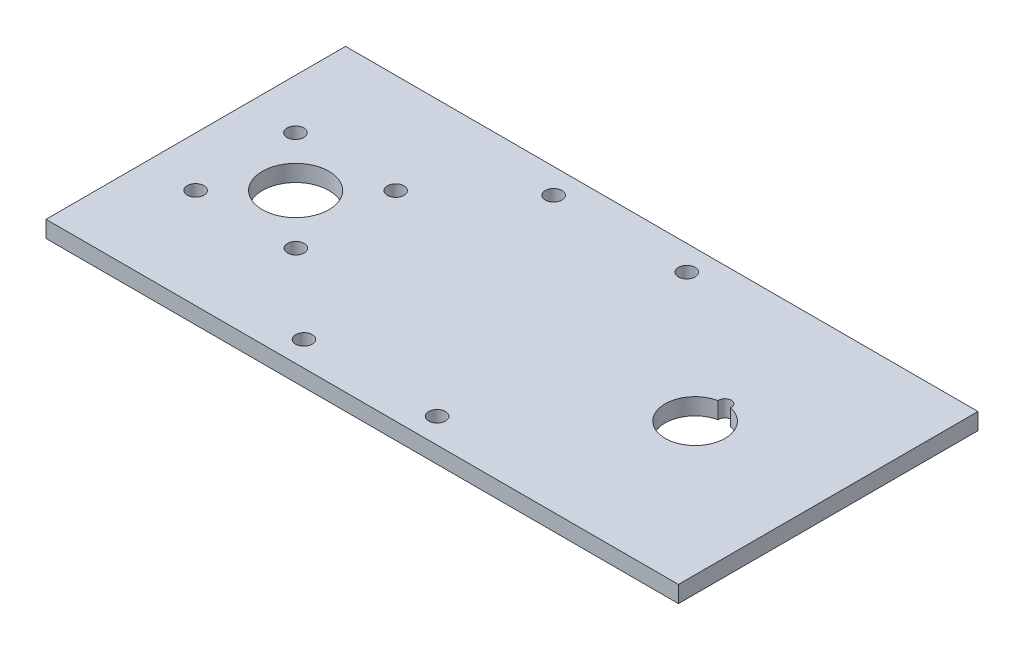
SolidWorks part; units mm, degrees
material "PC High Viscosity"
ref_plane "Front Plane" through (0, 0, 0) normal (0, 0, 1) x (1, 0, 0)
ref_plane "Top Plane" through (0, 0, 0) normal (0, 1, 0) x (1, 0, 0)
ref_plane "Right Plane" through (0, 0, 0) normal (1, 0, 0) x (0, 0, -1)
sketch "Sketch1" plane through (0, 0, 0) normal (0, 1, 0) x (1, 0, 0)
  line L1 (0, 0) -> (241.3, 0)
  line L2 (0, 0) -> (0, 114.3)
  line L3 (0, 114.3) -> (241.3, 114.3)
  line L4 (241.3, 0) -> (241.3, 114.3)
  circle A0 centre (38.1, 57.15) radius 12.7
  arc A1 (188.1317, 68.332) -> (192.8683, 68.332) centre (190.5, 57.15) ccw
  circle A2 centre (88.9, 104.775) radius 3.175
  circle A3 centre (139.7, 104.775) radius 3.175
  circle A4 centre (139.7, 9.525) radius 3.175
  circle A5 centre (88.9, 9.525) radius 3.175
  circle A6 centre (18.984, 76.2) radius 3.175
  circle A7 centre (18.984, 38.1) radius 3.175
  circle A8 centre (57.216, 38.1) radius 3.175
  circle A9 centre (57.216, 76.2) radius 3.175
  arc A10 (192.8683, 68.332) -> (188.1317, 68.332) centre (190.5, 68.58) ccw
  dimension "D1" = 25.4
  dimension "D2" = 22.86
  dimension "D9" = 6.35
  dimension "D15" = 6.35
  dimension "D19" = 4.7625
  dimension "D3" = 114.3
  dimension "D4" = 57.15
  dimension "D5" = 57.15
  dimension "D6" = 241.3
  dimension "D7" = 38.1
  dimension "D8" = 190.5
  dimension "D10" = 50.8
  dimension "D11" = 9.525
  dimension "D12" = 9.525
  dimension "D13" = 88.9
  dimension "D14" = 26.9875
  dimension "D16" = 26.9875
  dimension "D17" = 26.9875
  dimension "D18" = 38.1
extrude "Boss-Extrude1" add sketch "Sketch1" along normal blind 6.35
fillet "Fillet1" [suppressed] radius 6.35
fillet "Fillet2" [suppressed] radius 1.5875
